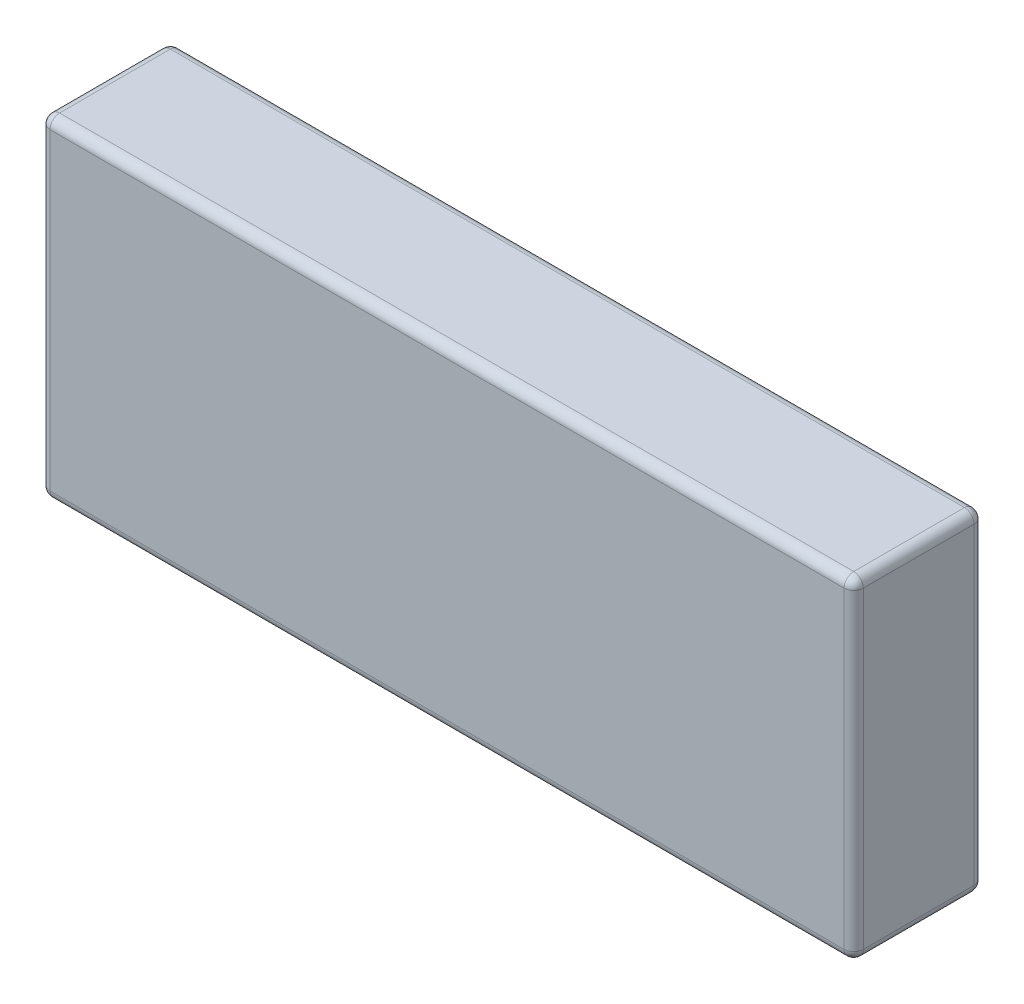
SolidWorks part; units mm, degrees
ref_plane "Front Plane" through (0, 0, 0) normal (0, 0, 1) x (1, 0, 0)
ref_plane "Top Plane" through (0, 0, 0) normal (0, 1, 0) x (1, 0, 0)
ref_plane "Right Plane" through (0, 0, 0) normal (1, 0, 0) x (0, 0, -1)
sketch "Sketch1" plane through (0, 0, 0) normal (0, 1, 0) x (1, 0, 0)
  line L1 (0, 0) -> (169, 0)
  line L2 (0, 0) -> (0, 27)
  line L3 (0, 27) -> (169, 27)
  line L4 (169, 0) -> (169, 27)
  dimension "D1" = 169
  dimension "D2" = 27
extrude "Boss-Extrude1" add sketch "Sketch1" along normal blind 69
fillet "Fillet1" radius 2 12 edges at (0, 34.5, 0) (169, 34.5, 0) (84.5, 0, 0) (169, 0, -13.5) (0, 0, -13.5) (169, 69, -13.5) (84.5, 69, 0) (0, 69, -13.5) (169, 34.5, -27) (84.5, 69, -27) (0, 34.5, -27) (84.5, 0, -27)
